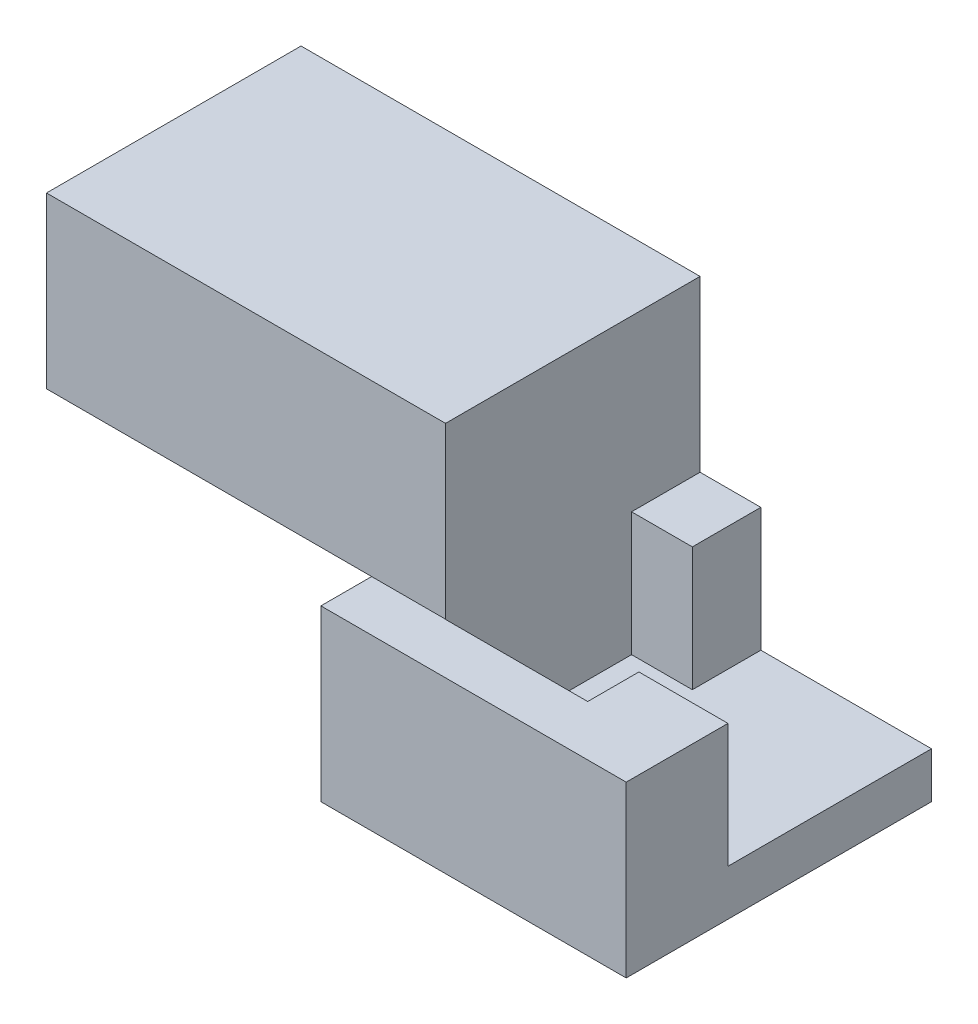
SolidWorks part; units mm, degrees
ref_plane "Front Plane" through (0, 0, 0) normal (0, 0, 1) x (1, 0, 0)
ref_plane "Top Plane" through (0, 0, 0) normal (0, 1, 0) x (1, 0, 0)
ref_plane "Right Plane" through (0, 0, 0) normal (1, 0, 0) x (0, 0, -1)
sketch "Sketch1" plane through (0, 0, 0) normal (0, 1, 0) x (1, 0, 0)
  line L1 (0, 0) -> (11.43, 0)
  line L2 (0, 0) -> (0, 11.43)
  line L3 (0, 11.43) -> (11.43, 11.43)
  line L4 (11.43, 0) -> (11.43, 11.43)
  dimension "D1" = 11.43
  dimension "D2" = 11.43
extrude "Boss-Extrude1" add sketch "Sketch1" along normal blind 6.35
sketch "Sketch3" plane through (0, 0, -11.43) normal (0, 0, -1) x (-1, 0, 0)
  line L0 (-11.43, 6.35) -> (0, 6.35) construction
  line L1 (-11.43, 6.35) -> (-5.0406, 6.35)
  line L2 (-11.43, 6.35) -> (-11.43, 1.718)
  line L3 (-11.43, 1.718) -> (-5.0406, 1.718)
  line L4 (-5.0406, 6.35) -> (-5.0406, 1.718)
  line L5 (-11.43, 6.35) -> (-11.43, 0) construction
  point P6 (-11.43, 1.718)
  point P9 (0, 0)
  point P10 (0, 0)
extrude "Cut-Extrude1" cut sketch "Sketch3" against normal blind 7.62
sketch "Sketch4" plane through (0, 1.718, 0) normal (0, 1, 0) x (1, 0, 0)
  line L1 (2.7656, 8.8657) -> (8.0958, 8.8657)
  line L2 (2.7656, 8.8657) -> (2.7656, 1.8931)
  line L3 (2.7656, 1.8931) -> (8.0958, 1.8931)
  line L4 (8.0958, 8.8657) -> (8.0958, 1.8931)
  point P4 (8.0958, 8.8657)
extrude "Cut-Extrude2" cut sketch "Sketch4" along normal blind 15.24
sketch "Sketch5" plane through (0, 6.35, 0) normal (0, 1, 0) x (1, 0, 0)
  line L1 (2.7656, 11.43) -> (-12.1729, 11.43)
  line L2 (2.7656, 11.43) -> (2.7656, 1.9005)
  line L3 (2.7656, 1.9005) -> (-12.1729, 1.9005)
  line L4 (-12.1729, 11.43) -> (-12.1729, 1.9005)
  point P5 (2.7656, 2.2801)
  point P6 (2.7656, 11.43)
  point P7 (-12.1729, 1.9005)
extrude "Boss-Extrude2" add sketch "Sketch5" along normal blind 6.35
